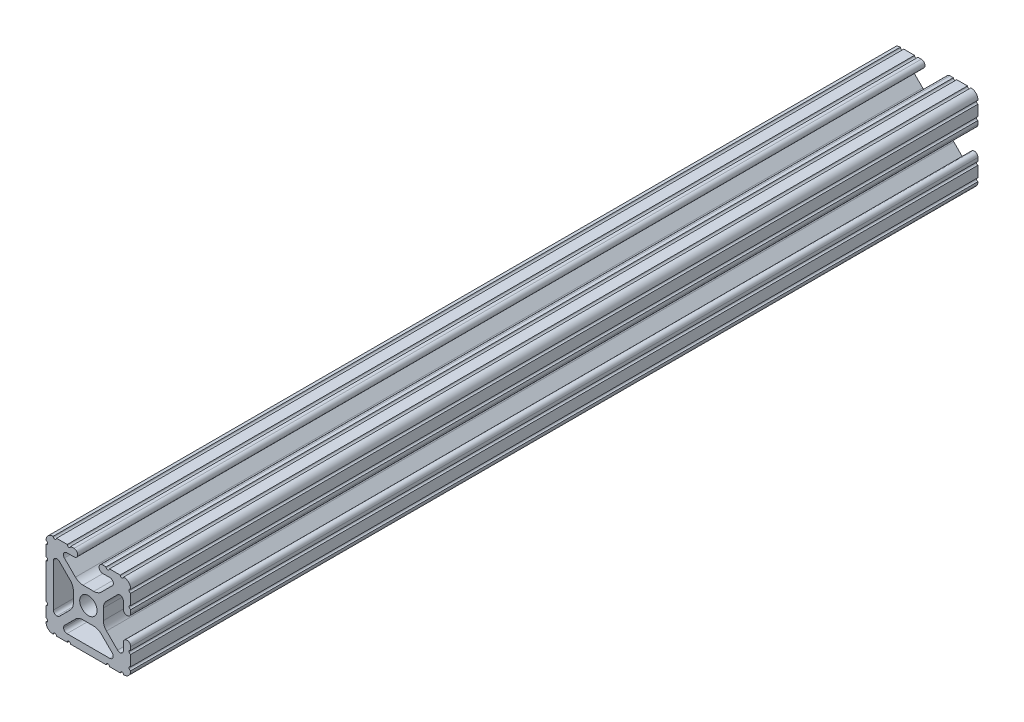
SolidWorks part; units mm, degrees
ref_plane "Front Plane" through (0, 0, 0) normal (0, 0, 1) x (1, 0, 0)
ref_plane "Top Plane" through (0, 0, 0) normal (0, 1, 0) x (1, 0, 0)
ref_plane "Right Plane" through (0, 0, 0) normal (1, 0, 0) x (0, 0, -1)
ref_plane "Plane1" through (0, 0, -558.8) normal (0, 0, -1) x (-1, 0, 0)
sketch "Sketch1" plane through (0, 0, -558.8) normal (0, 0, -1) x (-1, 0, 0)
  line L0 (12.7, -9.5504) -> (12.7, -6.3246)
  line L1 (12.7, -5.3086) -> (12.7, 5.3086)
  line L2 (12.7, 6.3246) -> (12.7, 9.5504)
  line L3 (9.5504, 12.7) -> (6.3246, 12.7)
  line L4 (5.3086, 12.7) -> (4.3023, 12.7)
  line L5 (4.3023, 10.4902) -> (6.4748, 10.4902)
  line L6 (7.1932, 8.7558) -> (3.8759, 5.4384)
  line L7 (1.6308, 4.5085) -> (-1.6308, 4.5085)
  line L8 (-3.8759, 5.4384) -> (-7.1932, 8.7558)
  line L9 (-6.4748, 10.4902) -> (-4.3023, 10.4902)
  line L10 (-4.3023, 12.7) -> (-5.3086, 12.7)
  line L11 (-6.3246, 12.7) -> (-9.5504, 12.7)
  line L12 (-12.7, 9.5504) -> (-12.7, 6.3246)
  line L13 (-12.7, 5.3086) -> (-12.7, 4.3023)
  line L14 (-10.4902, 4.3023) -> (-10.4902, 6.4748)
  line L15 (-8.7558, 7.1932) -> (-5.4384, 3.8759)
  line L16 (-4.5085, 1.6308) -> (-4.5085, -1.6308)
  line L17 (-5.4384, -3.8759) -> (-8.7558, -7.1932)
  line L18 (-10.4902, -6.4748) -> (-10.4902, -4.3023)
  line L19 (-12.7, -4.3023) -> (-12.7, -5.3086)
  line L20 (-12.7, -6.3246) -> (-12.7, -9.5504)
  line L21 (-9.5504, -12.7) -> (-6.3246, -12.7)
  line L22 (-5.3086, -12.7) -> (5.3086, -12.7)
  line L23 (6.3246, -12.7) -> (9.5504, -12.7)
  line L24 (3.8759, -5.4384) -> (7.1319, -8.6945)
  line L25 (6.4135, -10.4902) -> (-6.4135, -10.4902)
  line L26 (-7.1319, -8.6945) -> (-3.8759, -5.4384)
  line L27 (-1.6308, -4.5085) -> (1.6308, -4.5085)
  line L28 (10.4902, 6.4135) -> (10.4902, -6.4135)
  line L29 (8.6945, -7.1319) -> (5.4384, -3.8759)
  line L30 (4.5085, -1.6308) -> (4.5085, 1.6308)
  line L31 (5.4384, 3.8759) -> (8.6945, 7.1319)
  arc A0 (12.7, -10.5664) -> (12.7, -9.5504) centre (12.7, -10.0584) cw
  arc A1 (12.7, -6.3246) -> (12.7, -5.3086) centre (12.7, -5.8166) cw
  arc A2 (12.7, 5.3086) -> (12.7, 6.3246) centre (12.7, 5.8166) cw
  arc A3 (12.7, 9.5504) -> (12.7, 10.5664) centre (12.7, 10.0584) cw
  arc A4 (12.7, 10.5664) -> (10.5664, 12.7) centre (10.592, 10.592) ccw
  arc A5 (10.5664, 12.7) -> (9.5504, 12.7) centre (10.0584, 12.7) cw
  arc A6 (6.3246, 12.7) -> (5.3086, 12.7) centre (5.8166, 12.7) cw
  arc A7 (4.3023, 12.7) -> (4.3023, 10.4902) centre (4.3023, 11.5951) ccw
  arc A8 (6.4748, 10.4902) -> (7.1932, 8.7558) centre (6.4748, 9.4742) cw
  arc A9 (3.8759, 5.4384) -> (1.6308, 4.5085) centre (1.6308, 7.6835) cw
  arc A10 (-1.6308, 4.5085) -> (-3.8759, 5.4384) centre (-1.6308, 7.6835) cw
  arc A11 (-7.1932, 8.7558) -> (-6.4748, 10.4902) centre (-6.4748, 9.4742) cw
  arc A12 (-4.3023, 10.4902) -> (-4.3023, 12.7) centre (-4.3023, 11.5951) ccw
  arc A13 (-5.3086, 12.7) -> (-6.3246, 12.7) centre (-5.8166, 12.7) cw
  arc A14 (-9.5504, 12.7) -> (-10.5664, 12.7) centre (-10.0584, 12.7) cw
  arc A15 (-10.5664, 12.7) -> (-12.7, 10.5664) centre (-10.592, 10.592) ccw
  arc A16 (-12.7, 10.5664) -> (-12.7, 9.5504) centre (-12.7, 10.0584) cw
  arc A17 (-12.7, 6.3246) -> (-12.7, 5.3086) centre (-12.7, 5.8166) cw
  arc A18 (-12.7, 4.3023) -> (-10.4902, 4.3023) centre (-11.5951, 4.3023) ccw
  arc A19 (-10.4902, 6.4748) -> (-8.7558, 7.1932) centre (-9.4742, 6.4748) cw
  arc A20 (-5.4384, 3.8759) -> (-4.5085, 1.6308) centre (-7.6835, 1.6308) cw
  arc A21 (-4.5085, -1.6308) -> (-5.4384, -3.8759) centre (-7.6835, -1.6308) cw
  arc A22 (-8.7558, -7.1932) -> (-10.4902, -6.4748) centre (-9.4742, -6.4748) cw
  arc A23 (-10.4902, -4.3023) -> (-12.7, -4.3023) centre (-11.5951, -4.3023) ccw
  arc A24 (-12.7, -5.3086) -> (-12.7, -6.3246) centre (-12.7, -5.8166) cw
  arc A25 (-12.7, -9.5504) -> (-12.7, -10.5664) centre (-12.7, -10.0584) cw
  arc A26 (-12.7, -10.5664) -> (-10.5664, -12.7) centre (-10.592, -10.592) ccw
  arc A27 (-10.5664, -12.7) -> (-9.5504, -12.7) centre (-10.0584, -12.7) cw
  arc A28 (-6.3246, -12.7) -> (-5.3086, -12.7) centre (-5.8166, -12.7) cw
  arc A29 (5.3086, -12.7) -> (6.3246, -12.7) centre (5.8166, -12.7) cw
  arc A30 (9.5504, -12.7) -> (10.5664, -12.7) centre (10.0584, -12.7) cw
  arc A31 (10.5664, -12.7) -> (12.7, -10.5664) centre (10.592, -10.592) ccw
  circle A32 centre (0, 0) radius 2.6035
  arc A33 (7.1319, -8.6945) -> (7.4295, -9.4742) centre (6.2865, -9.4638) cw
  arc A34 (7.4295, -9.4742) -> (6.4135, -10.4902) centre (6.4135, -9.4742) cw
  arc A35 (-6.4135, -10.4902) -> (-7.4295, -9.4742) centre (-6.4135, -9.4742) cw
  arc A36 (-7.4295, -9.4742) -> (-7.1319, -8.6945) centre (-6.2865, -9.4638) cw
  arc A37 (-3.8759, -5.4384) -> (-1.6308, -4.5085) centre (-1.6308, -7.6835) cw
  arc A38 (1.6308, -4.5085) -> (3.8759, -5.4384) centre (1.6308, -7.6835) cw
  arc A39 (9.4742, 7.4295) -> (10.4902, 6.4135) centre (9.4742, 6.4135) cw
  arc A40 (10.4902, -6.4135) -> (9.4742, -7.4295) centre (9.4742, -6.4135) cw
  arc A41 (9.4742, -7.4295) -> (8.6945, -7.1319) centre (9.4638, -6.2865) cw
  arc A42 (5.4384, -3.8759) -> (4.5085, -1.6308) centre (7.6835, -1.6308) cw
  arc A43 (4.5085, 1.6308) -> (5.4384, 3.8759) centre (7.6835, 1.6308) cw
  arc A44 (8.6945, 7.1319) -> (9.4742, 7.4295) centre (9.4638, 6.2865) cw
extrude "Boss-Extrude1" add sketch "Sketch1" against normal blind 254
